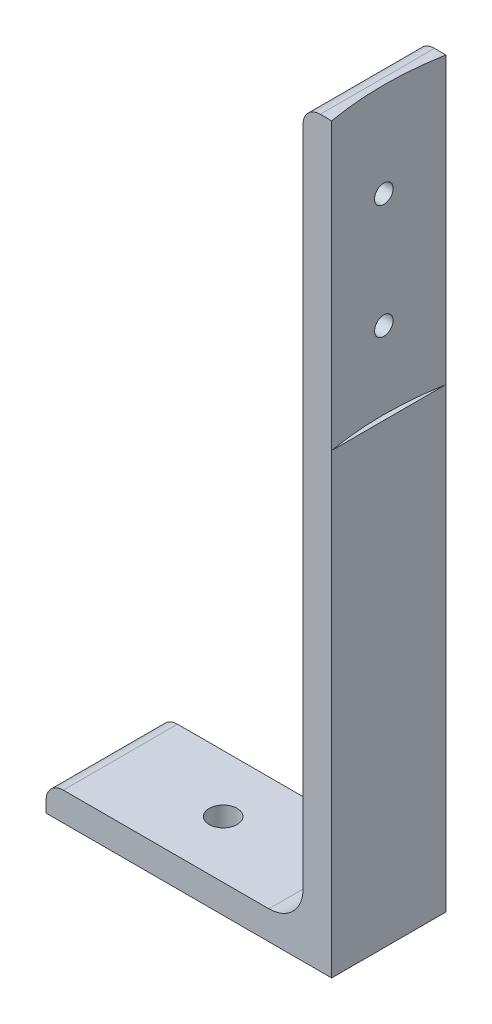
SolidWorks part; units mm, degrees
ref_plane "Front Plane" through (0, 0, 0) normal (0, 0, 1) x (1, 0, 0)
ref_plane "Top Plane" through (0, 0, 0) normal (0, 1, 0) x (1, 0, 0)
ref_plane "Right Plane" through (0, 0, 0) normal (1, 0, 0) x (0, 0, -1)
sketch "Sketch1" plane through (0, 0, 0) normal (0, 0, 1) x (1, 0, 0)
  line L0 (0, 0) -> (0, 130)
  line L1 (-2, 130) -> (0, 130)
  line L2 (-5, 127) -> (-5, 11)
  line L7 (-11, 5) -> (-47, 5)
  line L9 (0, 0) -> (-50, 0)
  line L10 (-50, 2) -> (-50, 0)
  arc A0 (-47, 5) -> (-50, 2) centre (-47, 2) ccw
  arc A1 (-2, 130) -> (-5, 127) centre (-2, 127) ccw
  arc A2 (-5, 11) -> (-11, 5) centre (-11, 11) cw
  point P0 (0, 0)
  point P15 (-5, 130)
  dimension "D1" = 3
  dimension "D6" = 3
  dimension "D7" = 6
  dimension "D2" = 5
  dimension "D3" = 5
  dimension "D4" = 130
  dimension "D5" = 50
extrude "Boss-Extrude1" add sketch "Sketch1" along normal mid plane 20
ref_plane "Plane1" through (0, 130, 0) normal (0, 1, 0) x (1, 0, 0)
sketch "Sketch2" plane through (0, 130, 0) normal (0, 1, 0) x (1, 0, 0)
  line L0 (0, -10) -> (0, 10) construction
  line L1 (0, -10) -> (0, 10)
  circle A0 centre (56.116, 0) radius 57
  dimension "D1" = 114
extrude "Cut-Extrude1" cut sketch "Sketch2" against normal blind 50 contours L1 A0
sketch "Sketch3" plane through (-5, 0, 0) normal (-1, 0, 0) x (0, 0, 1)
  line L0 (10, 80) -> (-10, 80) construction
  line L1 (10, 80) -> (-10, 80)
  line L2 (10, 127) -> (-10, 127) construction
  line L3 (10, 127) -> (-10, 127)
  line L4 (-10, 127) -> (-10, 80)
  line L5 (10, 127) -> (10, 80)
  line L6 (-10, 103.5) -> (10, 103.5) construction
  circle A0 centre (0, 113.5) radius 1.625
  circle A1 centre (0, 93.5) radius 1.625
  point P4 (0, 113.5)
  point P5 (0, 93.5)
  point P9 (0, 103.5)
  dimension "D2" = 3.25
  dimension "D3" = 3.25
  dimension "D1" = 10
extrude "Cut-Extrude2" cut sketch "Sketch3" against normal through all contours A1 | A0
sketch "Sketch8" plane through (0, 5, 0) normal (0, 1, 0) x (1, 0, 0)
  line L0 (-29, 10) -> (-29, -10) construction
  line L4 (-11, 10) -> (-47, 10)
  line L5 (-47, 10) -> (-47, -10)
  line L6 (-47, -10) -> (-11, -10)
  line L7 (-11, -10) -> (-11, 10)
  line L8 (-11, 10) -> (-47, 10)
  line L9 (-47, 10) -> (-47, -10)
  line L10 (-47, -10) -> (-11, -10)
  line L11 (-11, -10) -> (-11, 10)
  circle A0 centre (-29, 0) radius 2.45
  point P7 (-29, 10)
  point P10 (-29, -10)
  dimension "D2" = 4.9
  dimension "D1" = 0
extrude "Cut-Extrude3" cut sketch "Sketch8" against normal through all contours A0
